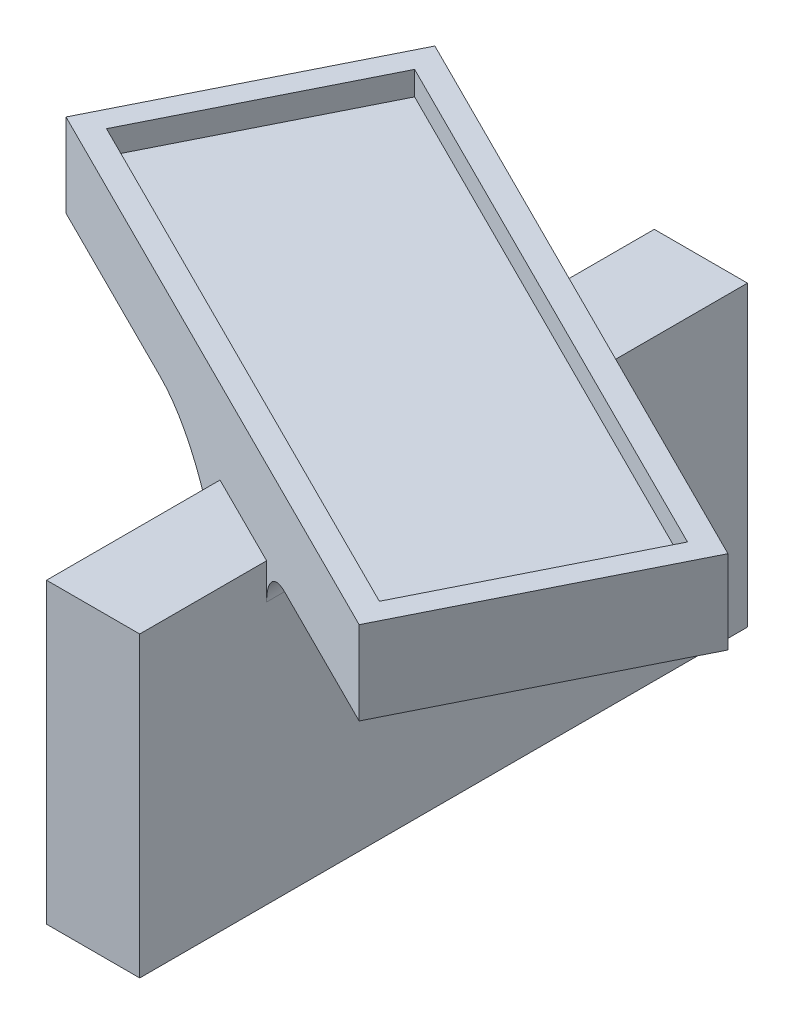
SolidWorks part; units mm, degrees
material "ABS"
ref_plane "Front Plane" through (0, 0, 0) normal (0, 0, 1) x (1, 0, 0)
ref_plane "Top Plane" through (0, 0, 0) normal (0, 1, 0) x (1, 0, 0)
ref_plane "Right Plane" through (0, 0, 0) normal (1, 0, 0) x (0, 0, -1)
sketch "Sketch1" plane through (0, 0, 0) normal (0, 1, 0) x (1, 0, 0)
  line L1 (-3.91, -25.5) -> (3.91, -25.5)
  line L2 (-3.91, -25.5) -> (-3.91, 25.5)
  line L3 (-3.91, 25.5) -> (3.91, 25.5)
  line L4 (3.91, -25.5) -> (3.91, 25.5)
  line L5 (-3.91, -25.5) -> (3.91, 25.5) construction
  line L6 (-3.91, 25.5) -> (3.91, -25.5) construction
  point P0 (0, 0)
extrude "Boss-Extrude1" add sketch "Sketch1" along normal blind 25
sketch "Sketch2" plane through (0, 25, 0) normal (0, 1, 0) x (1, 0, 0)
  line L0 (0, 0) -> (64.6527, 0) construction
  line L1 (-4.3382, -8.6764) -> (21.5791, 43.1582) construction
  line L2 (41.0151, -9.8471) -> (27.0721, -2.8756)
  line L3 (27.0721, -2.8756) -> (18.5437, -19.9323)
  line L4 (18.5437, -19.9323) -> (-27.0721, 2.8756)
  line L5 (-27.0721, 2.8756) -> (-18.5437, 19.9323)
  line L6 (-18.5437, 19.9323) -> (41.0151, -9.8471)
  line L7 (-18.5437, 19.9323) -> (18.5437, -19.9323) construction
  line L8 (27.0721, -2.8756) -> (-27.0721, 2.8756) construction
  line L9 (-29.7554, 1.9812) -> (19.4381, -22.6156)
  line L10 (-3.91, -25.5) -> (3.91, -25.5) construction
  line L11 (19.4381, -22.6156) -> (29.7554, -1.9812)
  line L12 (29.7554, -1.9812) -> (-19.4381, 22.6156)
  line L13 (-19.4381, 22.6156) -> (-29.7554, 1.9812)
  point P5 (0, 0)
  point P12 (0, 0)
  dimension "D1" = 25.5
  dimension "D2" = 51
  dimension "D3" = 25.5
  dimension "D4" = 90
  dimension "D5" = 0
  dimension "D7" = 19.07
  dimension "D8" = 2
  dimension "D9" = 2
  dimension "D10" = 2
  dimension "D11" = 2
extrude "Boss-Extrude2" add sketch "Sketch2" along normal blind 5 contours L12 L13 L9 L11
sketch "Sketch3" plane through (0, 30, 0) normal (0, 1, 0) x (1, 0, 0)
  line L0 (-19.4381, 22.6156) -> (-29.7554, 1.9812) construction
  line L1 (29.7554, -1.9812) -> (-19.4381, 22.6156) construction
  line L2 (19.4381, -22.6156) -> (29.7554, -1.9812) construction
  line L4 (19.4381, -22.6156) -> (29.7554, -1.9812)
  line L5 (29.7554, -1.9812) -> (-19.4381, 22.6156)
  line L6 (-19.4381, 22.6156) -> (-29.7554, 1.9812)
  line L7 (-29.7554, 1.9812) -> (19.4381, -22.6156)
  line L11 (-29.7554, 1.9812) -> (19.4381, -22.6156)
  line L18 (-18.5884, 20.0665) -> (27.2062, -2.8309)
  line L19 (27.2062, -2.8309) -> (18.5884, -20.0665)
  line L20 (18.5884, -20.0665) -> (-27.2062, 2.8309) construction
  line L21 (-27.2062, 2.8309) -> (-18.5884, 20.0665)
  line M5 (19.4381, -22.6156) -> (29.7554, -1.9812)
  line M6 (29.7554, -1.9812) -> (-19.4381, 22.6156)
  line M7 (-19.4381, 22.6156) -> (-29.7554, 1.9812)
  line M8 (-29.7554, 1.9812) -> (19.4381, -22.6156)
  dimension "D2" = 1.9
  dimension "D3" = 1.9
  dimension "D4" = 1.9
  dimension "D5" = 1.9
  dimension "D1" = 0
extrude "Boss-Extrude3" add sketch "Sketch3" along normal blind 2 contours L20 L21 L18 L19 M8 M5 M6 M7
fillet "Fillet1" radius 10 1 edges at (-3.91, 25, -1.955)
fillet "Fillet2" radius 3 1 edges at (3.91, 25, 1.955)
sketch "Sketch4" plane through (-3.91, 0, 0) normal (-1, 0, 0) x (0, 0, 1)
  line L1 (-1.5, -5) -> (1.5, -5)
  line L2 (-1.5, -5) -> (-1.5, 5)
  line L3 (-1.5, 5) -> (1.5, 5)
  line L4 (1.5, -5) -> (1.5, 5)
  line L5 (-1.5, -5) -> (1.5, 5) construction
  line L6 (-1.5, 5) -> (1.5, -5) construction
  line L7 (-25.5, 0) -> (25.5, 0) construction
  point P6 (0, 0)
  point P7 (0, 0)
  dimension "D1" = 0
extrude "Boss-Extrude4" add sketch "Sketch4" along normal blind 2.5
chamfer "Chamfer1" distance 1 angle 45 3 edges at (-3.91, 2.5, -1.5) (-3.91, 5, 0) (-3.91, 2.5, 1.5)
